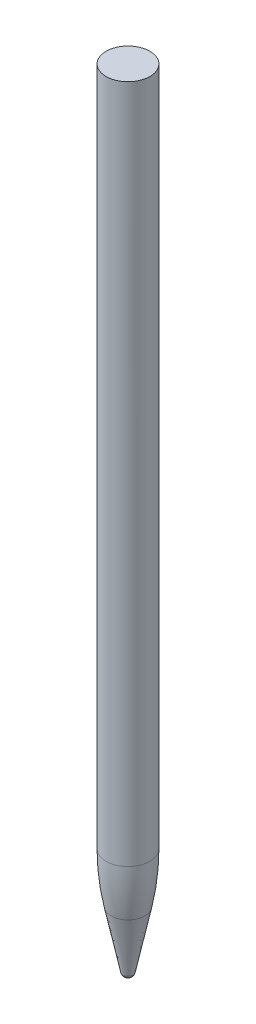
SolidWorks part; units mm, degrees
material "ABS"
ref_plane "Front Plane" through (0, 0, 0) normal (0, 0, 1) x (1, 0, 0)
ref_plane "Top Plane" through (0, 0, 0) normal (0, 1, 0) x (1, 0, 0)
ref_plane "Right Plane" through (0, 0, 0) normal (1, 0, 0) x (0, 0, -1)
sketch "Sketch1" plane through (0, 0, 0) normal (0, 0, 1) x (1, 0, 0)
  line L1 (4.425, 18) -> (4.425, 160.5)
  line L2 (4.425, 160.5) -> (0, 160.5)
  line L3 (0, 0.7136) -> (0.875, 0.7136) construction
  line L4 (4.425, 18) -> (0.875, 0.7136)
  line L5 (0, 160.5) -> (0, 0)
  arc A0 (0, 0) -> (0.875, 0.7136) centre (0, 0.8933) ccw
  point P2 (0, 0)
  point P6 (0, 0)
  point P8 (0.875, 1.0106)
  point P10 (0, 0)
  point P11 (0, 0)
  dimension "D1" = 4.425
  dimension "D2" = 0.875
  dimension "D3" = 160.5
  dimension "D4" = 18
revolve "Revolve1" add sketch "Sketch1" angle 360 about L5
fillet "Fillet1" radius 1 1 edges at (0, 0.7136, 0.875)
fillet "Fillet2" radius 50 1 edges at (0, 18, 4.425)
